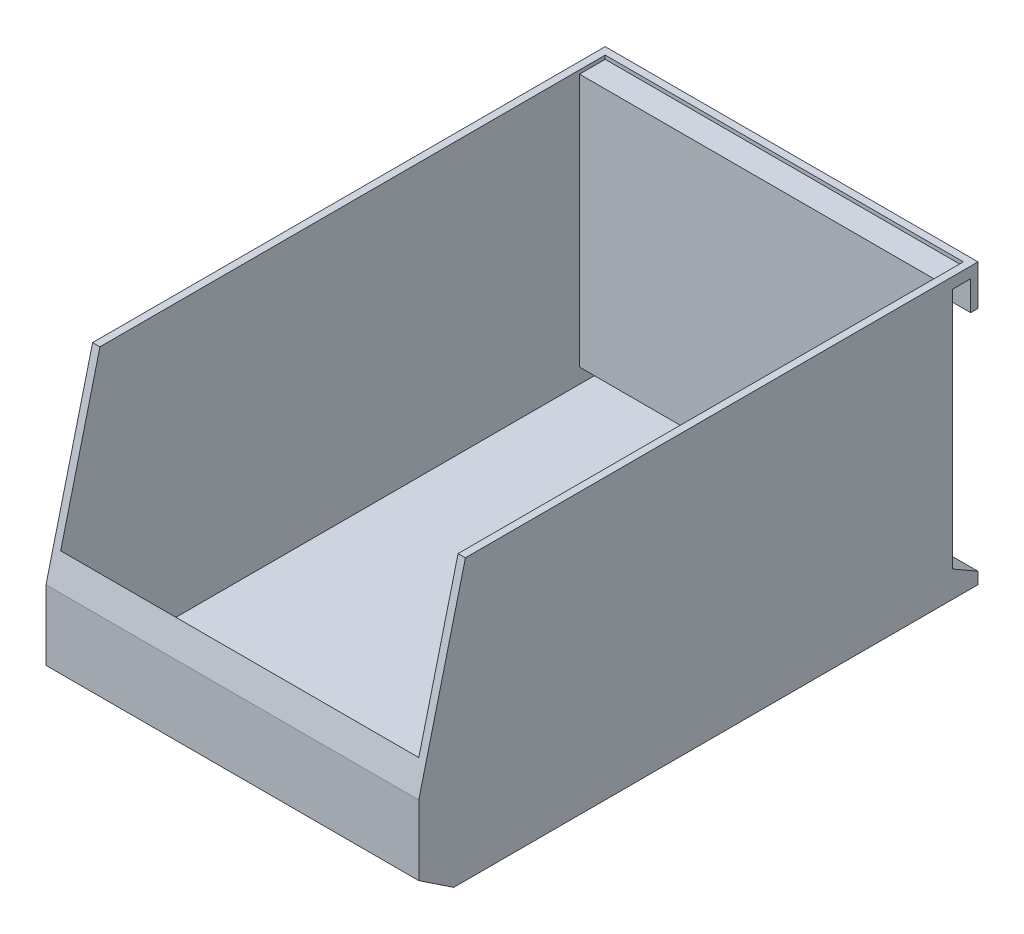
SolidWorks part; units mm, degrees
ref_plane "Front Plane" through (0, 0, 0) normal (0, 0, 1) x (1, 0, 0)
ref_plane "Top Plane" through (0, 0, 0) normal (0, 1, 0) x (1, 0, 0)
ref_plane "Right Plane" through (0, 0, 0) normal (1, 0, 0) x (0, 0, -1)
sketch "Sketch1" plane through (0, 0, 0) normal (0, 1, 0) x (1, 0, 0)
  line L1 (-50.8, -76.2) -> (50.8, -76.2)
  line L2 (-50.8, -76.2) -> (-50.8, 76.2)
  line L3 (-50.8, 76.2) -> (50.8, 76.2)
  line L4 (50.8, -76.2) -> (50.8, 76.2)
  line L5 (-50.8, -76.2) -> (50.8, 76.2) construction
  line L6 (-50.8, 76.2) -> (50.8, -76.2) construction
  point P0 (0, 0)
  dimension "D1" = 152.4
  dimension "D2" = 101.6
extrude "Boss-Extrude1" add sketch "Sketch1" along normal blind 76.2
sketch "Sketch2" plane through (50.8, 0, 0) normal (1, 0, 0) x (0, 0, -1)
  line L0 (-63.5, 76.2) -> (-76.2, 25.4)
  line L1 (-76.2, 76.2) -> (76.2, 76.2) construction
  line L2 (-76.2, 76.2) -> (-76.2, 0) construction
  line L3 (-76.2, 6.35) -> (-76.2, 0)
  line L4 (-76.2, 6.35) -> (-66.675, 0)
  line L5 (-76.2, 0) -> (76.2, 0) construction
  line L6 (-76.2, 0) -> (-66.675, 0)
  line L7 (-76.2, 25.4) -> (-76.2, 76.2)
  line L8 (-76.2, 76.2) -> (-63.5, 76.2)
  dimension "D1" = 12.7
  dimension "D2" = 9.525
  dimension "D3" = 19.05
  dimension "D4" = 6.35
extrude "Cut-Extrude1" cut sketch "Sketch2" against normal through all
sketch "Sketch3" plane through (50.8, 0, 0) normal (1, 0, 0) x (0, 0, -1)
  line L0 (76.2, 76.2) -> (76.2, 0) construction
  line L1 (76.2, 7.2165) -> (69.2, 7.2165) construction
  line L3 (76.2, 65.2) -> (69.2, 65.2) construction
  line L4 (69.2, 7.2165) -> (69.2, 65.2)
  line L5 (69.2, 7.2165) -> (76.2, 3.175)
  line L6 (69.2, 65.2) -> (69.2, 73.2)
  line L7 (69.2, 73.2) -> (74.2, 73.2)
  line L8 (74.2, 73.2) -> (74.2, 65.2)
  line L9 (74.2, 65.2) -> (76.2, 65.2)
  line L10 (76.2, 65.2) -> (76.2, 3.175)
  line L11 (-63.5, 76.2) -> (76.2, 76.2) construction
  dimension "D1" = 7
  dimension "D2" = 3.175
  dimension "D3" = 30
  dimension "D4" = 2
  dimension "D5" = 3
  dimension "D6" = 8
extrude "Cut-Extrude2" cut sketch "Sketch3" against normal through all
shell "Shell1" thickness 2
